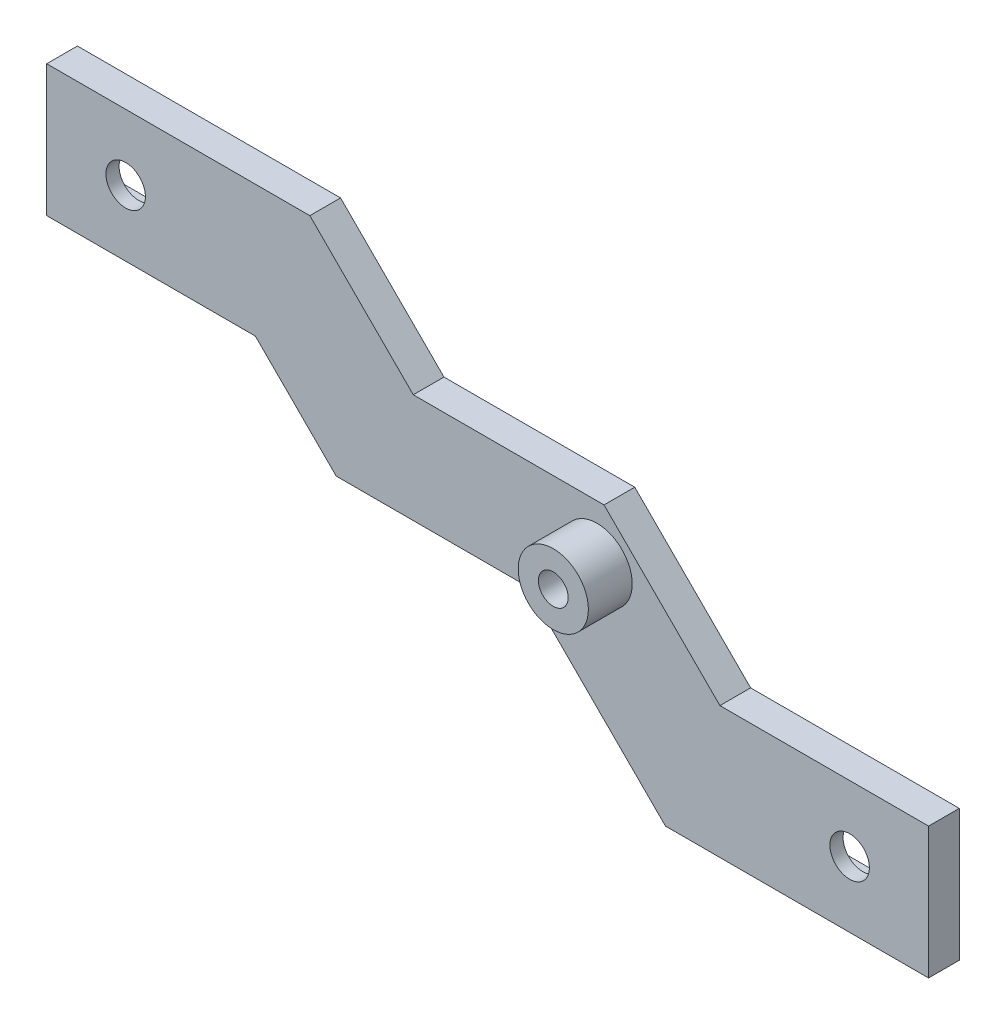
SolidWorks part; units mm, degrees
ref_plane "Спереди" through (0, 0, 0) normal (0, 0, 1) x (1, 0, 0)
ref_plane "Сверху" through (0, 0, 0) normal (0, 1, 0) x (1, 0, 0)
ref_plane "Справа" through (0, 0, 0) normal (1, 0, 0) x (0, 0, -1)
sketch "Эскиз1" plane through (0, 0, 0) normal (0, 0, 1) x (1, 0, 0)
  line L1 (112.7696, -7.5) -> (12.2304, -7.5)
  line L2 (112.7696, -7.5) -> (112.7696, 32.5)
  line L3 (112.7696, 32.5) -> (12.2304, 32.5)
  line L4 (12.2304, -7.5) -> (12.2304, 32.5)
  line L9 (32.7304, 21.5) -> (15.7304, 21.5)
  line L10 (32.7304, 21.5) -> (32.7304, 28.5)
  line L11 (32.7304, 28.5) -> (15.7304, 28.5)
  line L12 (15.7304, 21.5) -> (15.7304, 28.5)
  line L14 (16.2304, 22) -> (32.2304, 22) construction
  line L17 (50.7696, -3.5) -> (110.7696, -3.5) construction
  line L20 (110.7696, 3.5) -> (50.7696, 3.5) construction
  line L21 (109.2696, -3.5) -> (92.2696, -3.5)
  line L22 (109.2696, -3.5) -> (109.2696, 3.5)
  line L23 (109.2696, 3.5) -> (92.2696, 3.5)
  line L24 (92.2696, -3.5) -> (92.2696, 3.5)
  line L25 (108.7696, -3) -> (108.7696, 3) construction
  line L26 (92.7696, 3) -> (92.7696, -3) construction
  dimension "D1" = 0.5
  dimension "D2" = 17
  dimension "D3" = 7
  dimension "D4" = 0.5
  dimension "D5" = 0.5
extrude "Бобышка-Вытянуть1" add sketch "Эскиз1" along normal blind 2
sketch "Эскиз2" plane through (0, 0, 2) normal (0, 0, 1) x (1, 0, 0)
  line L1 (12.2304, 32.5) -> (112.7696, 32.5)
  line L2 (12.2304, 32.5) -> (12.2304, -7.5)
  line L3 (12.2304, -7.5) -> (112.7696, -7.5)
  line L4 (112.7696, 32.5) -> (112.7696, -7.5)
  circle A0 centre (21.2304, 25) radius 2.25
  circle A1 centre (103.7696, 0) radius 2.25
extrude "Бобышка-Вытянуть2" add sketch "Эскиз2" along normal blind 1.5
sketch "Эскиз3" plane through (0, 0, 3.5) normal (0, 0, 1) x (1, 0, 0)
  line L0 (12.2304, 32.5) -> (42.2304, 32.5)
  line L1 (112.7696, 32.5) -> (12.2304, 32.5) construction
  line L2 (42.2304, 32.5) -> (54.0204, 20.71)
  line L3 (54.0204, 20.71) -> (75.7696, 20.71)
  line L4 (75.7696, 20.71) -> (88.9796, 7.5)
  line L5 (88.9796, 7.5) -> (112.7696, 7.5)
  line L6 (112.7696, -7.5) -> (112.7696, 32.5) construction
  line L7 (112.7696, 7.5) -> (112.7696, -7.5)
  line L8 (112.7696, -7.5) -> (82.7696, -7.5)
  line L9 (12.2304, -7.5) -> (112.7696, -7.5) construction
  line L10 (82.7696, -7.5) -> (66.9828, 8.2868)
  line L11 (66.9828, 8.2868) -> (45.2304, 8.2868)
  line L12 (45.2304, 8.2868) -> (36.0172, 17.5)
  line L13 (36.0172, 17.5) -> (12.2304, 17.5)
  line L14 (12.2304, 32.5) -> (12.2304, -7.5) construction
  line L15 (12.2304, 17.5) -> (12.2304, 32.5)
  line L17 (-11.173, 55.2443) -> (173.6359, 55.2443)
  line L18 (-11.173, 55.2443) -> (-11.173, -39.5809)
  line L19 (-11.173, -39.5809) -> (173.6359, -39.5809)
  line L20 (173.6359, 55.2443) -> (173.6359, -39.5809)
  circle A0 centre (103.7696, 0) radius 1.25 construction
  circle A1 centre (21.2304, 25) radius 1.25 construction
  dimension "D4" = 7.5
  dimension "D1" = 45
  dimension "D2" = 45
  dimension "D3" = 7.5
  dimension "D5" = 7.5
  dimension "D6" = 45
  dimension "D7" = 15
  dimension "D8" = 30
  dimension "D9" = 30
  dimension "D10" = 23.7868
  dimension "D11" = 23.79
  dimension "D12" = 14.9977
  dimension "D13" = 33
  dimension "D14" = 37
extrude "Вырез-Вытянуть1" cut sketch "Эскиз3" against normal blind 31.5
sketch "Эскиз4" plane through (0, 0, 3.5) normal (0, 0, 1) x (1, 0, 0)
  line L1 (42.2304, 32.5) -> (12.2304, 32.5) construction
  line L3 (12.2304, 32.5) -> (12.2304, 17.5) construction
  circle A0 centre (32.2304, 28.5) radius 3.5
  point P5 (21.2304, 25)
  dimension "D1" = 7
  dimension "D3" = 20
  dimension "D2" = 4
extrude "Бобышка-Вытянуть3" [suppressed] add sketch "Эскиз4" along normal blind 10
sketch "Эскиз5" plane through (0, 0, 3.5) normal (0, 0, 1) x (1, 0, 0)
  line L0 (75.7696, 20.71) -> (54.0204, 20.71) construction
  line L1 (45.2304, 8.2868) -> (66.9828, 8.2868) construction
  line L2 (74.9828, 14.5) -> (63.7868, 14.5) construction
  line L4 (66.9828, 8.2868) -> (66.9828, 18.6399) construction
  circle A0 centre (74.9828, 14.5) radius 4
  dimension "D1" = 8
  dimension "D2" = 6.21
  dimension "D3" = 6.2132
  dimension "D4" = 6.2132
  dimension "D5" = 6.2132
  dimension "D6" = 8
extrude "Бобышка-Вытянуть4" add sketch "Эскиз5" along normal blind 5
sketch "Эскиз6" plane through (0, 0, 8.5) normal (0, 0, 1) x (1, 0, 0)
  circle A0 centre (74.9828, 14.5) radius 1.7
  dimension "D1" = 3.4
extrude "Вырез-Вытянуть2" cut sketch "Эскиз6" against normal blind 10
